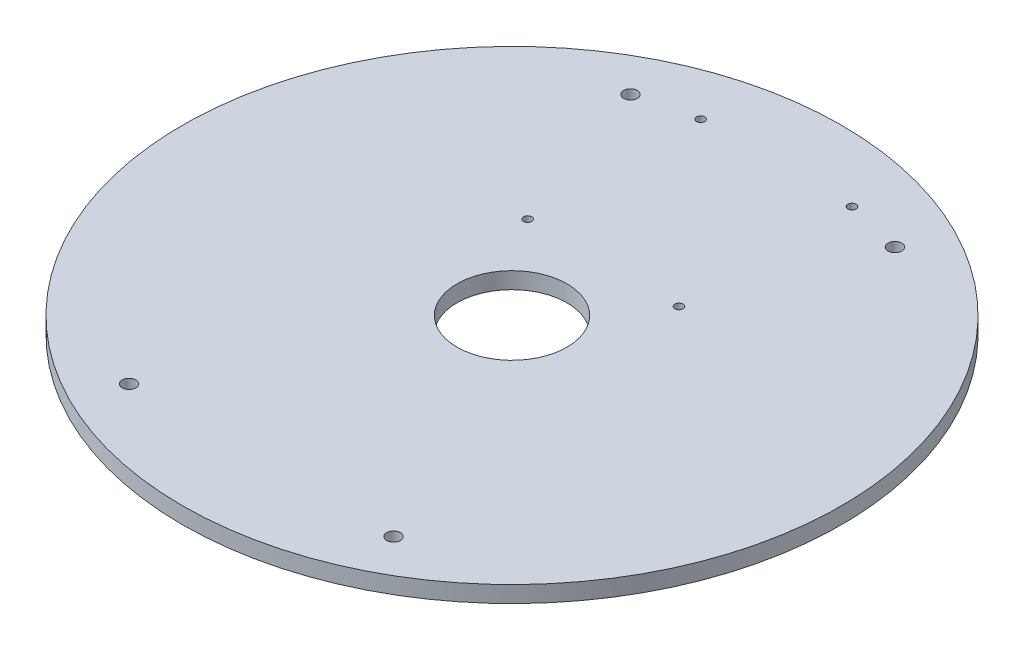
SolidWorks part; units mm, degrees
ref_plane "Front Plane" through (0, 0, 0) normal (0, 0, 1) x (1, 0, 0)
ref_plane "Top Plane" through (0, 0, 0) normal (0, 1, 0) x (1, 0, 0)
ref_plane "Right Plane" through (0, 0, 0) normal (1, 0, 0) x (0, 0, -1)
sketch "Sketch1" plane through (0, 0, 0) normal (0, 1, 0) x (1, 0, 0)
  circle A0 centre (0, 0) radius 60
  dimension "D1" = 120
extrude "Boss-Extrude1" add sketch "Sketch1" along normal blind 3
sketch "Sketch2" plane through (0, 3, 0) normal (0, 1, 0) x (1, 0, 0)
  line L0 (0, 60) -> (0, -60) construction
  line L1 (-60, 0) -> (60, 0) construction
  line L2 (-42.3936, -29.0021) -> (42.6064, -29.0021) construction
  line L3 (-42.3936, 29.0021) -> (42.6064, 29.0021) construction
  circle A0 centre (0, 0) radius 60 construction
  circle A5 centre (0, 0) radius 51.6037 construction
  circle A6 centre (-24.0731, 45.6446) radius 1.25
  circle A7 centre (24.0731, 45.6446) radius 1.25
  circle A8 centre (24.0731, -45.6446) radius 1.25
  circle A9 centre (-24.0731, -45.6446) radius 1.25
  dimension "D4" = 2.5
  dimension "D1" = 85
extrude "Cut-Extrude1" cut sketch "Sketch2" against normal through all
sketch "Sketch4" plane through (0, 3, 0) normal (0, 1, 0) x (1, 0, 0)
  line L0 (0, 0) -> (60, 0) construction
  line L1 (24.6, 12.9) -> (58.5968, 12.9)
  line L2 (24.6, 12.9) -> (24.6, -12.9)
  line L3 (60, 0) -> (24.6, 0)
  line L4 (0, 60) -> (0, -60) construction
  line L5 (24.6, -12.9) -> (58.5968, -12.9)
  line L6 (-24.6, -12.9) -> (-58.5968, -12.9)
  line L7 (-24.6, 12.9) -> (-24.6, -12.9)
  line L8 (-24.6, 12.9) -> (-58.5968, 12.9)
  circle A0 centre (0, 0) radius 60 construction
  dimension "D1" = 12.9
  dimension "D2" = 35.4
sketch "Sketch5" plane through (0, 3, 0) normal (0, 1, 0) x (1, 0, 0)
  circle A0 centre (0, 0) radius 10
extrude "Cut-Extrude2" cut sketch "Sketch5" against normal through all
sketch "Sketch6" plane through (0, 3, 0) normal (0, 1, 0) x (1, 0, 0)
  line L4 (0, 60) -> (0, -60) construction
  circle A0 centre (13.7737, 48.1208) radius 0.75
  circle A1 centre (13.7737, 16.6208) radius 0.75
  circle A2 centre (-13.7737, 16.6208) radius 0.75
  circle A3 centre (-13.7737, 48.1208) radius 0.75
  dimension "D5" = 1.5
extrude "Cut-Extrude3" cut sketch "Sketch6" against normal through all
